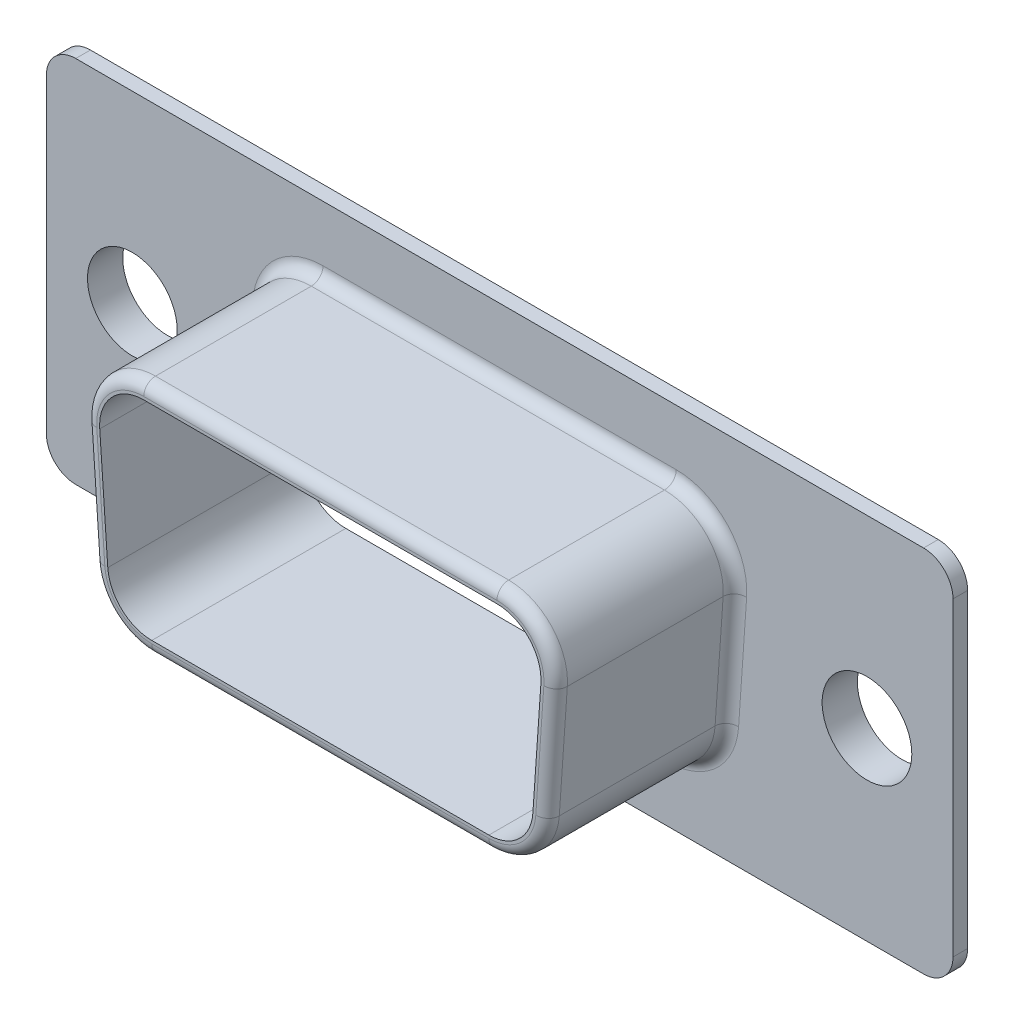
SolidWorks part; units mm, degrees
ref_plane "Front Plane" through (0, 0, 0) normal (0, 0, 1) x (1, 0, 0)
ref_plane "Top Plane" through (0, 0, 0) normal (0, 1, 0) x (1, 0, 0)
ref_plane "Right Plane" through (0, 0, 0) normal (1, 0, 0) x (0, 0, -1)
sketch "Sketch1" plane through (0, 0, 0) normal (0, 0, 1) x (1, 0, 0)
  line L1 (-14.42, 6.275) -> (14.42, 6.275)
  line L2 (-15.42, 5.275) -> (-15.42, -5.275)
  line L3 (-14.42, -6.275) -> (14.42, -6.275)
  line L4 (15.42, 5.275) -> (15.42, -5.275)
  line L5 (0, -6.275) -> (0, 6.275) construction
  line L6 (-15.42, 0) -> (15.42, 0) construction
  arc A0 (14.42, 6.275) -> (15.42, 5.275) centre (14.42, 5.275) cw
  arc A1 (15.42, -5.275) -> (14.42, -6.275) centre (14.42, -5.275) cw
  arc A2 (-15.42, -5.275) -> (-14.42, -6.275) centre (-14.42, -5.275) ccw
  arc A3 (-15.42, 5.275) -> (-14.42, 6.275) centre (-14.42, 5.275) cw
  point P0 (0, 0)
  point P6 (15.42, 6.275)
  point P10 (15.42, -6.275)
  point P15 (-15.42, 6.275)
  dimension "D3" = 1
  dimension "D1" = 30.84
  dimension "D2" = 12.55
extrude "Boss-Extrude1" add sketch "Sketch1" along normal blind 0.5
sketch "Sketch2" plane through (0, 0, 0.5) normal (0, 0, 1) x (1, 0, 0)
  line L0 (-15.42, 0) -> (15.42, 0) construction
  line L1 (-15.42, 5.275) -> (-15.42, -5.275) construction
  line L2 (15.42, -5.275) -> (15.42, 5.275) construction
  circle A0 centre (-12.495, 0) radius 1.525
  circle A1 centre (12.495, 0) radius 1.525
  dimension "D2" = 3.05
  dimension "D3" = 3.05
  dimension "D1" = 2.925
  dimension "D4" = 2.925
  dimension "D5" = 24.99
extrude "Cut-Extrude1" cut sketch "Sketch2" against normal up to surface (0.5 mm away) up to face at (0, 0, 0)
sketch "Sketch3" plane through (0, 0, 0.5) normal (0, 0, 1) x (1, 0, 0)
  line L0 (-15.42, 0) -> (15.42, 0) construction
  line L1 (-15.42, 5.275) -> (-15.42, -5.275) construction
  line L2 (15.42, -5.275) -> (15.42, 5.275) construction
  line L3 (-6.0069, 3.975) -> (6.0069, 3.975)
  line L4 (0, -6.275) -> (0, 6.275) construction
  line L5 (-14.42, -6.275) -> (14.42, -6.275) construction
  line L6 (14.42, 6.275) -> (-14.42, 6.275) construction
  line L7 (-5.7336, -3.975) -> (5.7336, -3.975)
  line L8 (8.15, 3.975) -> (8.15, -3.95) construction
  line L9 (-8.15, 3.975) -> (-8.15, -3.925) construction
  line L10 (8.0021, 1.837) -> (7.7288, -2.113)
  line L11 (-8.0021, 1.837) -> (-7.7288, -2.113)
  line L12 (-8.15, 3.975) -> (-8.15, 10.0936) construction
  arc A2 (7.7288, -2.113) -> (5.7336, -3.975) centre (5.7336, -1.975) cw
  arc A3 (-5.7336, -3.975) -> (-7.7288, -2.113) centre (-5.7336, -1.975) cw
  arc A4 (8.0021, 1.837) -> (6.0069, 3.975) centre (6.0069, 1.975) ccw
  arc A5 (-8.0021, 1.837) -> (-6.0069, 3.975) centre (-6.0069, 1.975) cw
  point P14 (0, 3.975)
  point P28 (7.6, -3.975)
  point P31 (-7.6, -3.975)
  dimension "D7" = 2
  dimension "D1" = 3.975
  dimension "D2" = 16.3
  dimension "D3" = 3.975
  dimension "D4" = 15.2
  dimension "D5" = 3.958
extrude "Boss-Extrude2" add sketch "Sketch3" along normal blind 6.1
sketch "Sketch9" plane through (0, 0, 0) normal (0, 0, -1) x (-1, 0, 0)
  line L0 (-14.02, 0) -> (-14.32, 0) construction
  circle A0 centre (-12.495, 0) radius 1.525 construction
  circle A1 centre (-12.495, 0) radius 1.525
  circle A2 centre (12.495, 0) radius 1.525 construction
  circle A3 centre (12.495, 0) radius 1.525
  circle A4 centre (-12.495, 0) radius 1.825
  circle A5 centre (12.495, 0) radius 1.825
  dimension "D1" = 3.05
  dimension "D3" = 3.65
  dimension "D4" = 3.65
  dimension "D2" = 0.3
extrude "Boss-Extrude3" add sketch "Sketch9" along normal blind 0.5
sketch "Sketch10" plane through (0, 0, -0.5) normal (0, 0, -1) x (-1, 0, 0)
  line L0 (-14.02, 0) -> (-14.52, 0) construction
  circle A0 centre (-12.495, 0) radius 1.525 construction
  circle A1 centre (-12.495, 0) radius 1.525
  circle A2 centre (12.495, 0) radius 1.525 construction
  circle A3 centre (12.495, 0) radius 1.525
  circle A4 centre (-12.495, 0) radius 2.025
  circle A5 centre (12.495, 0) radius 2.025
  dimension "D2" = 4.05
  dimension "D3" = 4.05
  dimension "D1" = 0.5
extrude "Boss-Extrude4" add sketch "Sketch10" along normal blind 0.2
sketch "Sketch11" plane through (0, 0, 6.6) normal (0, 0, 1) x (1, 0, 0)
  line L8 (-7.5033, 1.8715) -> (-7.23, -2.0785)
  line L9 (-5.7336, -3.475) -> (5.7336, -3.475)
  line L10 (7.23, -2.0785) -> (7.5033, 1.8715)
  line L11 (6.0069, 3.475) -> (-6.0069, 3.475)
  line L12 (-7.5033, 1.8715) -> (-7.23, -2.0785)
  line L13 (-5.7336, -3.475) -> (5.7336, -3.475)
  line L14 (7.23, -2.0785) -> (7.5033, 1.8715)
  line L15 (6.0069, 3.475) -> (-6.0069, 3.475)
  arc A8 (-7.23, -2.0785) -> (-5.7336, -3.475) centre (-5.7336, -1.975) ccw
  arc A9 (5.7336, -3.475) -> (7.23, -2.0785) centre (5.7336, -1.975) ccw
  arc A10 (7.5033, 1.8715) -> (6.0069, 3.475) centre (6.0069, 1.975) ccw
  arc A11 (-6.0069, 3.475) -> (-7.5033, 1.8715) centre (-6.0069, 1.975) ccw
  arc A12 (-7.23, -2.0785) -> (-5.7336, -3.475) centre (-5.7336, -1.975) ccw
  arc A13 (5.7336, -3.475) -> (7.23, -2.0785) centre (5.7336, -1.975) ccw
  arc A14 (7.5033, 1.8715) -> (6.0069, 3.475) centre (6.0069, 1.975) ccw
  arc A15 (-6.0069, 3.475) -> (-7.5033, 1.8715) centre (-6.0069, 1.975) ccw
  dimension "D1" = 0.5
extrude "Cut-Extrude2" cut sketch "Sketch11" against normal up to surface (6.6 mm away) up to face at (10.67, 0, 0)
fillet "Fillet1" radius 0.4 8 edges at (-7.0981, -3.4372, 6.6) (-7.8655, -0.138, 6.6) (-7.4691, 3.3395, 6.6) (0, 3.975, 6.6) (7.4691, 3.3395, 6.6) (7.8655, -0.138, 6.6) (7.0981, -3.4372, 6.6) (0, -3.975, 6.6)
fillet "Fillet2" radius 0.4 8 edges at (-7.0981, -3.4372, 0.5) (-7.8655, -0.138, 0.5) (-7.4691, 3.3395, 0.5) (0, 3.975, 0.5) (7.4691, 3.3395, 0.5) (7.8655, -0.138, 0.5) (7.0981, -3.4372, 0.5) (0, -3.975, 0.5)
